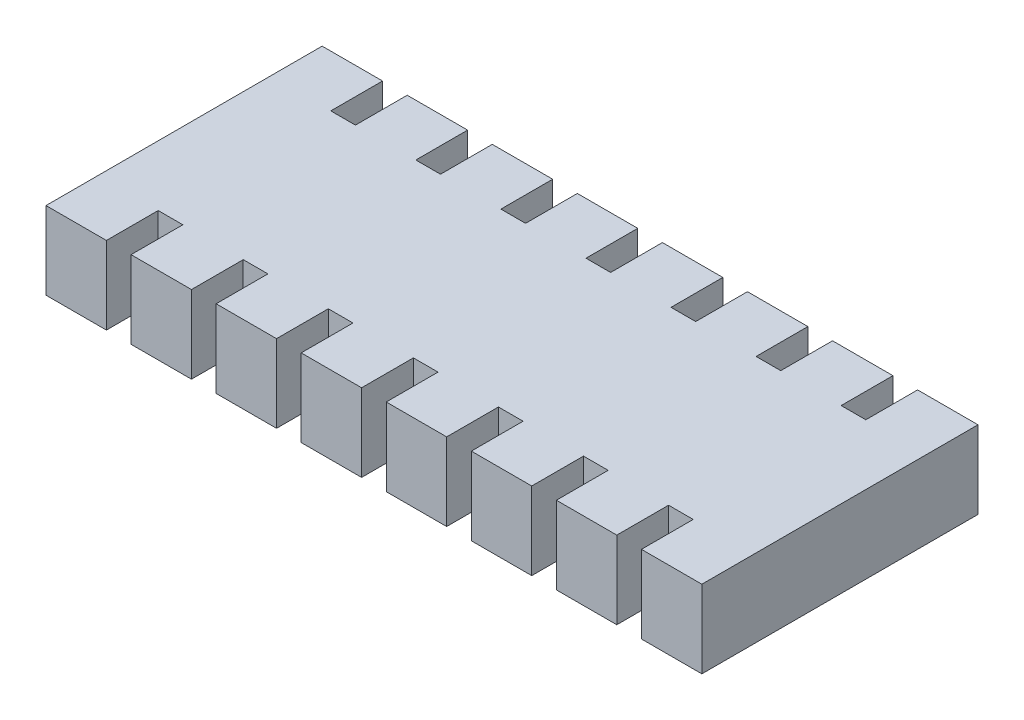
SolidWorks part; units mm, degrees
ref_plane "Front Plane" through (0, 0, 0) normal (0, 0, 1) x (1, 0, 0)
ref_plane "Top Plane" through (0, 0, 0) normal (0, 1, 0) x (1, 0, 0)
ref_plane "Right Plane" through (0, 0, 0) normal (1, 0, 0) x (0, 0, -1)
sketch "Sketch1" plane through (0, 0, 0) normal (0, 1, 0) x (1, 0, 0)
  line L1 (-1.9, 0.5) -> (1.9, 0.5)
  line L2 (-1.9, 0.5) -> (-1.9, -0.5)
  line L3 (-1.9, -0.5) -> (1.9, -0.5)
  line L4 (1.9, 0.5) -> (1.9, -0.5)
  line L5 (-1.9, 0.5) -> (1.9, -0.5) construction
  line L6 (-1.9, -0.5) -> (1.9, 0.5) construction
  point P0 (0, 0)
  dimension "D1" = 1
  dimension "D2" = 3.8
extrude "Boss-Extrude1" add sketch "Sketch1" along normal blind 0.45
sketch "Sketch2" plane through (0, 0.45, 0) normal (0, 1, 0) x (1, 0, 0)
  line L0 (-1.4071, 0.5) -> (-1.0571, 0.5)
  line L1 (-1.9, 0.5) -> (-1.55, 0.5)
  line L2 (-1.9, 0.5) -> (-1.9, 0.8)
  line L3 (-1.9, 0.8) -> (-1.55, 0.8)
  line L4 (-1.55, 0.5) -> (-1.55, 0.8)
  line L5 (-1.4071, 0.5) -> (-1.4071, 0.8)
  line L6 (-1.4071, 0.8) -> (-1.0571, 0.8)
  line L7 (-1.0571, 0.5) -> (-1.0571, 0.8)
  line L8 (-0.9143, 0.5) -> (-0.5643, 0.5)
  line L9 (-0.9143, 0.5) -> (-0.9143, 0.8)
  line L10 (-0.9143, 0.8) -> (-0.5643, 0.8)
  line L11 (-0.5643, 0.5) -> (-0.5643, 0.8)
  line L12 (-0.4214, 0.5) -> (-0.0714, 0.5)
  line L13 (-0.4214, 0.5) -> (-0.4214, 0.8)
  line L14 (-0.4214, 0.8) -> (-0.0714, 0.8)
  line L15 (-0.0714, 0.5) -> (-0.0714, 0.8)
  line L16 (0.0714, 0.5) -> (0.4214, 0.5)
  line L17 (0.0714, 0.5) -> (0.0714, 0.8)
  line L18 (0.0714, 0.8) -> (0.4214, 0.8)
  line L19 (0.4214, 0.5) -> (0.4214, 0.8)
  line L20 (0.5643, 0.5) -> (0.9143, 0.5)
  line L21 (0.5643, 0.5) -> (0.5643, 0.8)
  line L22 (0.5643, 0.8) -> (0.9143, 0.8)
  line L23 (0.9143, 0.5) -> (0.9143, 0.8)
  line L24 (1.0571, 0.5) -> (1.4071, 0.5)
  line L25 (1.0571, 0.5) -> (1.0571, 0.8)
  line L26 (1.0571, 0.8) -> (1.4071, 0.8)
  line L27 (1.4071, 0.5) -> (1.4071, 0.8)
  line L28 (1.55, 0.5) -> (1.9, 0.5)
  line L29 (1.55, 0.5) -> (1.55, 0.8)
  line L30 (1.55, 0.8) -> (1.9, 0.8)
  line L31 (1.9, 0.5) -> (1.9, 0.8)
  line L32 (-1.9, 0.5) -> (-1.4071, 0.5) construction
  line L33 (1.9, -0.5) -> (1.9, 0.5) construction
  line L34 (-1.9, 0) -> (1.9, 0) construction
  line L35 (-1.9, 0.5) -> (-1.9, -0.5) construction
  line L36 (-1.9, -0.5) -> (-1.4071, -0.5) construction
  line L37 (1.9, -0.5) -> (1.9, -0.8)
  line L38 (1.55, -0.8) -> (1.9, -0.8)
  line L39 (1.55, -0.5) -> (1.55, -0.8)
  line L40 (1.55, -0.5) -> (1.9, -0.5)
  line L41 (1.4071, -0.5) -> (1.4071, -0.8)
  line L42 (1.0571, -0.8) -> (1.4071, -0.8)
  line L43 (1.0571, -0.5) -> (1.0571, -0.8)
  line L44 (1.0571, -0.5) -> (1.4071, -0.5)
  line L45 (0.9143, -0.5) -> (0.9143, -0.8)
  line L46 (0.5643, -0.8) -> (0.9143, -0.8)
  line L47 (0.5643, -0.5) -> (0.5643, -0.8)
  line L48 (0.5643, -0.5) -> (0.9143, -0.5)
  line L49 (0.4214, -0.5) -> (0.4214, -0.8)
  line L50 (0.0714, -0.8) -> (0.4214, -0.8)
  line L51 (0.0714, -0.5) -> (0.0714, -0.8)
  line L52 (0.0714, -0.5) -> (0.4214, -0.5)
  line L53 (-0.0714, -0.5) -> (-0.0714, -0.8)
  line L54 (-0.4214, -0.8) -> (-0.0714, -0.8)
  line L55 (-0.4214, -0.5) -> (-0.4214, -0.8)
  line L56 (-0.4214, -0.5) -> (-0.0714, -0.5)
  line L57 (-0.5643, -0.5) -> (-0.5643, -0.8)
  line L58 (-0.9143, -0.8) -> (-0.5643, -0.8)
  line L59 (-0.9143, -0.5) -> (-0.9143, -0.8)
  line L60 (-0.9143, -0.5) -> (-0.5643, -0.5)
  line L61 (-1.0571, -0.5) -> (-1.0571, -0.8)
  line L62 (-1.4071, -0.8) -> (-1.0571, -0.8)
  line L63 (-1.4071, -0.5) -> (-1.4071, -0.8)
  line L64 (-1.55, -0.5) -> (-1.55, -0.8)
  line L65 (-1.9, -0.8) -> (-1.55, -0.8)
  line L66 (-1.9, -0.5) -> (-1.9, -0.8)
  line L67 (-1.9, -0.5) -> (-1.55, -0.5)
  line L68 (-1.4071, -0.5) -> (-1.0571, -0.5)
  dimension "D1" = 0.3
  dimension "D2" = 0.35
  dimension "D3" = 8
extrude "Boss-Extrude2" add sketch "Sketch2" against normal up to surface (0.45 mm away) up to face at (0, 0, 0)
